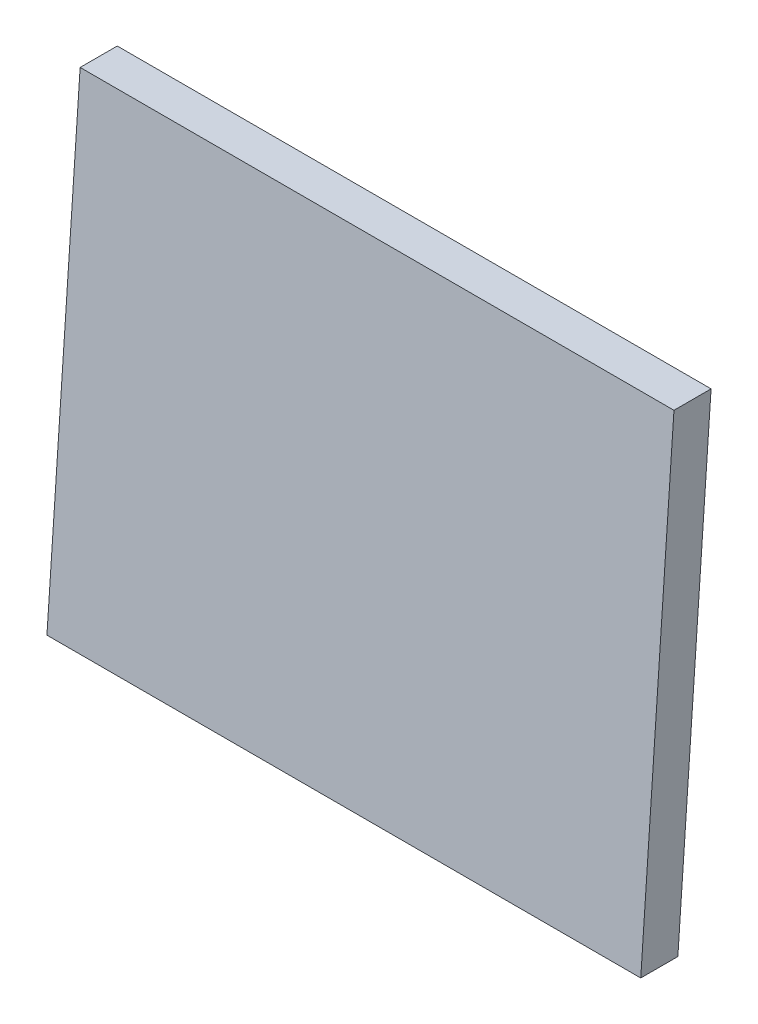
SolidWorks part; units mm, degrees
other "Markup1"
sketch "Sketch2" plane through (0, 320, -22.3766) normal (-0.79, 0.322, -0.5217) x (-0.5064, 0.1369, 0.8514)
sketch "Sketch3" plane through (0, 320, -22.3766) normal (-0.79, 0.322, -0.5217) x (-0.5064, 0.1369, 0.8514)
ref_plane "Front Plane" through (0, 0, 0) normal (0, 0, 1) x (1, 0, 0)
ref_plane "Top Plane" through (0, 0, 0) normal (0, 1, 0) x (1, 0, 0)
ref_plane "Right Plane" through (0, 0, 0) normal (1, 0, 0) x (0, 0, -1)
sketch "Sketch1" plane through (0, 0, 0) normal (1, 0, 0) x (0, 0, -1)
  line L0 (-25, 0) -> (0, 0)
  line L1 (0, 0) -> (22.3766, 320)
  line L2 (22.3766, 320) -> (-2.6234, 320)
  line L3 (-2.6234, 320) -> (-25, 0)
  dimension "D1" = 94
  dimension "D2" = 86
  dimension "D3" = 25
  dimension "D4" = 320
extrude "Boss-Extrude1" add sketch "Sketch1" along normal blind 400 contours L3 L0 L1 L2
